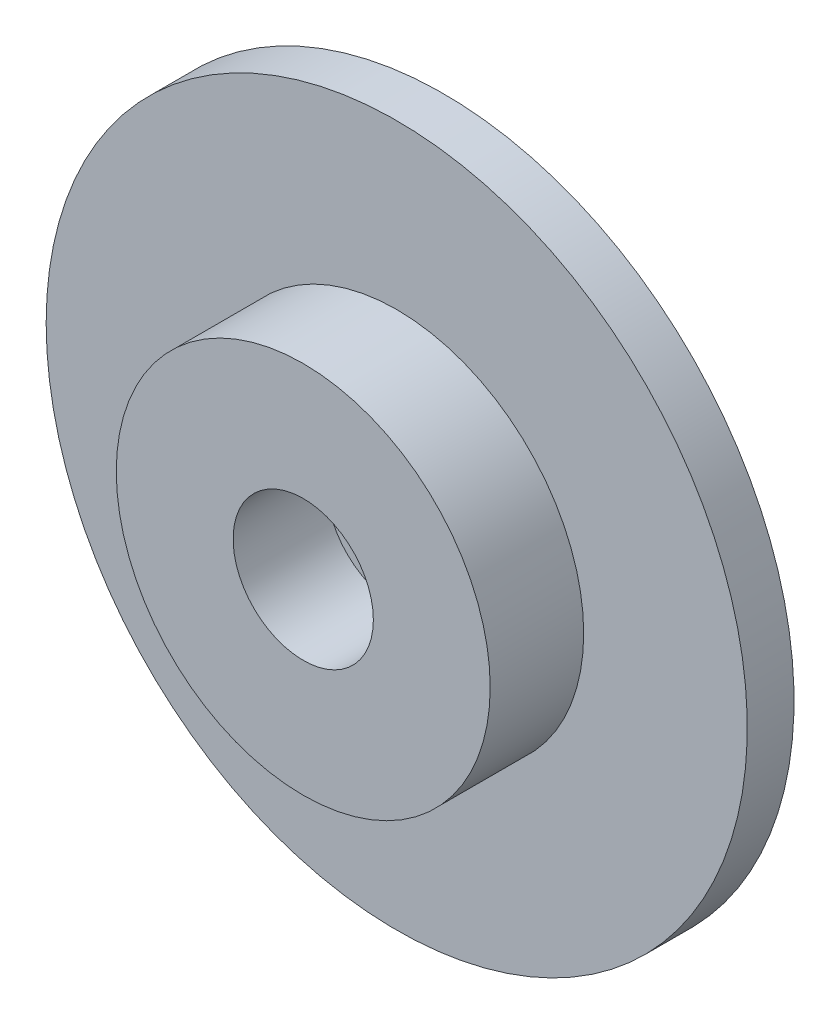
SolidWorks part; units mm, degrees
ref_plane "Plan de face" through (0, 0, 0) normal (0, 0, 1) x (1, 0, 0)
ref_plane "Plan de dessus" through (0, 0, 0) normal (0, 1, 0) x (1, 0, 0)
ref_plane "Plan de droite" through (0, 0, 0) normal (1, 0, 0) x (0, 0, -1)
sketch "Esquisse1" plane through (0, 0, 0) normal (0, 0, 1) x (1, 0, 0)
  circle A0 centre (0, 0) radius 4
extrude "Boss.-Extru.1" add sketch "Esquisse1" along normal blind 2
sketch "Esquisse2" plane through (0, 0, 2) normal (0, 0, 1) x (1, 0, 0)
  circle A0 centre (0, 0) radius 1.5
extrude "Enlèv. mat.-Extru.1" cut sketch "Esquisse2" against normal blind 2.5
sketch "Esquisse3" plane through (0, 0, 0) normal (0, 0, -1) x (-1, 0, 0)
  circle A0 centre (0, 0) radius 7.5
extrude "Boss.-Extru.2" add sketch "Esquisse3" along normal blind 1
